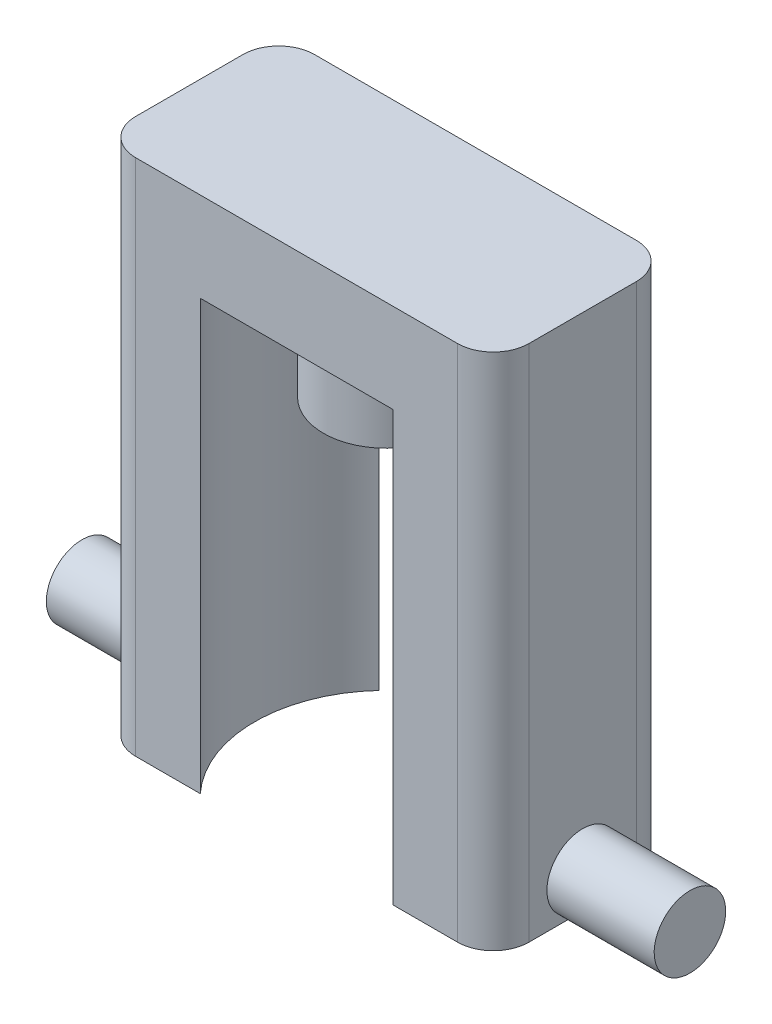
SolidWorks part; units mm, degrees
ref_plane "Front Plane" through (0, 0, 0) normal (0, 0, 1) x (1, 0, 0)
ref_plane "Top Plane" through (0, 0, 0) normal (0, 1, 0) x (1, 0, 0)
ref_plane "Right Plane" through (0, 0, 0) normal (1, 0, 0) x (0, 0, -1)
sketch "Sketch1" plane through (0, 0, 0) normal (0, 1, 0) x (1, 0, 0)
  line L1 (-13.97, 6.35) -> (13.97, 6.35)
  line L2 (-13.97, 6.35) -> (-13.97, -6.35)
  line L3 (-13.97, -6.35) -> (13.97, -6.35)
  line L4 (13.97, 6.35) -> (13.97, -6.35)
  point P5 (0, 6.35)
  point P7 (13.97, 0)
  dimension "D1" = 27.94
  dimension "D2" = 12.7
extrude "Boss-Extrude1" add sketch "Sketch1" along normal blind 6.35
sketch "Sketch2" plane through (0, 0, 0) normal (0, -1, 0) x (1, 0, 0)
  line L5 (0, -76.1102) -> (0, 76.1102) construction
  circle A0 centre (0, 0) radius 4.445
  point P12 (0, 0)
  dimension "D1" = 8.89
extrude "Boss-Extrude2" add sketch "Sketch2" along normal blind 5.842
sketch "Sketch3" plane through (0, 0, 0) normal (0, -1, 0) x (1, 0, 0)
  line L0 (0, -15.4177) -> (0, 18.9618) construction
  line L1 (-13.97, -6.35) -> (-13.97, 6.35)
  line L2 (-13.97, 6.35) -> (-6.8418, 6.35)
  line L3 (-13.97, 6.35) -> (13.97, 6.35) construction
  line L4 (-6.8418, -6.35) -> (-13.97, -6.35)
  line L5 (13.97, -6.35) -> (-13.97, -6.35) construction
  line L6 (6.8418, -6.35) -> (13.97, -6.35)
  line L7 (13.97, 6.35) -> (6.8418, 6.35)
  line L8 (13.97, -6.35) -> (13.97, 6.35)
  arc A0 (-6.8418, 6.35) -> (-6.8418, -6.35) centre (0, 0) ccw
  arc A1 (6.8418, 6.35) -> (6.8418, -6.35) centre (0, 0) cw
  dimension "D1" = 18.669
extrude "Boss-Extrude3" add sketch "Sketch3" along normal blind 30.48
sketch "Sketch4" plane through (-13.97, 0, 0) normal (-1, 0, 0) x (0, 0, 1)
  line L0 (6.35, -30.48) -> (-6.35, -30.48) construction
  line L1 (-6.35, 6.35) -> (6.35, 6.35) construction
  circle A0 centre (0, -27.94) radius 2.54
  point P4 (0, 0)
  point P7 (0, 6.35)
  dimension "D1" = 5.08
extrude "Boss-Extrude4" add sketch "Sketch4" along normal blind 7.62
sketch "Sketch5" plane through (13.97, 0, 0) normal (1, 0, 0) x (0, 0, -1)
  line L0 (6.35, -30.48) -> (-6.35, -30.48) construction
  line L1 (-6.35, 6.35) -> (6.35, 6.35) construction
  circle A0 centre (0, -27.94) radius 2.54
  point P4 (0, 0)
  point P7 (0, 6.35)
  dimension "D1" = 5.08
extrude "Boss-Extrude5" add sketch "Sketch5" along normal blind 7.62
fillet "Fillet1" radius 2.54 4 edges at (-13.97, -12.065, -6.35) (-13.97, -12.065, 6.35) (13.97, -12.065, -6.35) (13.97, -12.065, 6.35)
